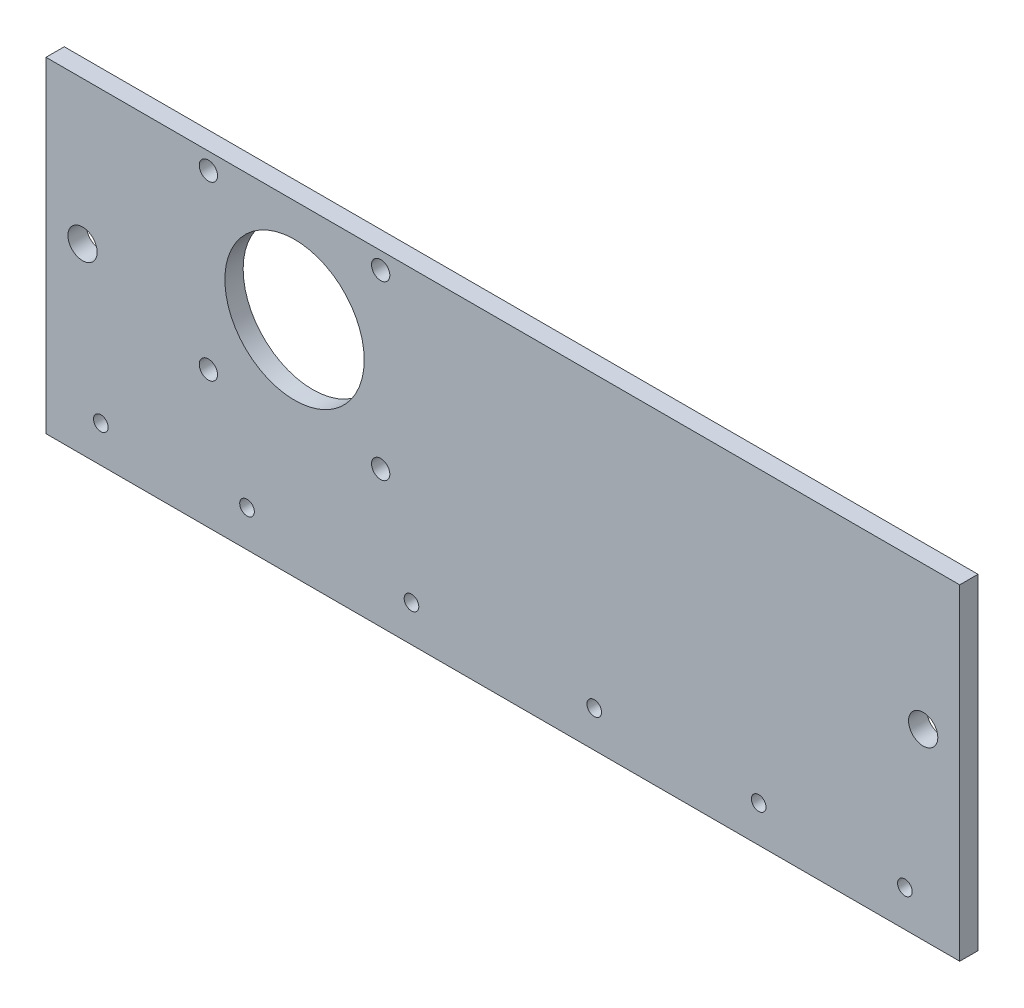
SolidWorks part; units mm, degrees
ref_plane "Ebene vorne" through (0, 0, 0) normal (0, 0, 1) x (1, 0, 0)
ref_plane "Ebene oben" through (0, 0, 0) normal (0, 1, 0) x (1, 0, 0)
ref_plane "Ebene rechts" through (0, 0, 0) normal (1, 0, 0) x (0, 0, -1)
sketch "Skizze1" plane through (0, 0, 0) normal (0, 0, 1) x (1, 0, 0)
  line L1 (0, 0) -> (250, 0)
  line L2 (0, 0) -> (0, 89.2)
  line L3 (0, 89.2) -> (250, 89.2)
  line L4 (250, 0) -> (250, 89.2)
  dimension "D1" = 250
  dimension "D2" = 89.2
extrude "Aufsatz-Linear austragen1" add sketch "Skizze1" against normal blind 5
sketch "Skizze2" plane through (0, 0, 0) normal (0, 0, 1) x (1, 0, 0)
  line L0 (0, 0) -> (250, 0) construction
  line L2 (250, 0) -> (250, 89.2) construction
  circle A0 centre (68, 61) radius 19.0625
  dimension "D1" = 38.125
  dimension "D2" = 61
  dimension "D3" = 182
extrude "Schnitt-Linear austragen1" cut sketch "Skizze2" against normal blind 27
sketch "Skizze3" plane through (0, 0, 0) normal (0, 0, 1) x (1, 0, 0)
  line L0 (0, 89.2) -> (0, 0) construction
  line L1 (0, 0) -> (250, 0) construction
  line L2 (250, 0) -> (250, 89.2) construction
  circle A0 centre (15, 10) radius 2
  circle A1 centre (55, 10) radius 2
  circle A2 centre (195, 10) radius 2
  circle A3 centre (235, 10) radius 2
  circle A4 centre (150, 10) radius 2
  dimension "D1" = 4
  dimension "D8" = 4
  dimension "D2" = 15
  dimension "D3" = 10
  dimension "D4" = 15
  dimension "D5" = 55
  dimension "D6" = 55
  dimension "D7" = 10
  dimension "D9" = 100
extrude "Schnitt-Linear austragen2" cut sketch "Skizze3" against normal blind 10
sketch "Skizze4" plane through (0, 0, 0) normal (0, 0, 1) x (1, 0, 0)
  line L0 (0, 89.2) -> (0, 0) construction
  line L1 (250, 0) -> (250, 89.2) construction
  line L2 (0, 0) -> (250, 0) construction
  circle A0 centre (10, 50) radius 4
  circle A1 centre (240, 50) radius 4
  dimension "D4" = 8
  dimension "D1" = 10
  dimension "D2" = 10
  dimension "D3" = 50
extrude "Schnitt-Linear austragen3" cut sketch "Skizze4" against normal blind 10
sketch "Skizze5" plane through (0, 0, 0) normal (0, 0, 1) x (1, 0, 0)
  line L0 (250, 89.2) -> (0, 89.2) construction
  line L1 (250, 0) -> (250, 89.2) construction
  line L2 (0, 89.2) -> (0, 0) construction
  circle A0 centre (44.43, 84.57) radius 2.5
  circle A1 centre (91.57, 84.57) radius 2.5
  circle A2 centre (91.57, 37.43) radius 2.5
  circle A3 centre (44.43, 37.43) radius 2.5
  dimension "D1" = 5
  dimension "D2" = 4.63
  dimension "D3" = 158.43
  dimension "D4" = 47.14
  dimension "D5" = 44.43
extrude "Schnitt-Linear austragen4" cut sketch "Skizze5" against normal blind 10
sketch "Skizze6" plane through (0, 0, 0) normal (0, 0, 1) x (1, 0, 0)
  line L0 (0, 0) -> (250, 0) construction
  line L1 (0, 89.2) -> (0, 0) construction
  circle A0 centre (100, 10) radius 2
  dimension "D3" = 4
  dimension "D1" = 10
  dimension "D2" = 100
extrude "Schnitt-Linear austragen5" cut sketch "Skizze6" against normal blind 10
